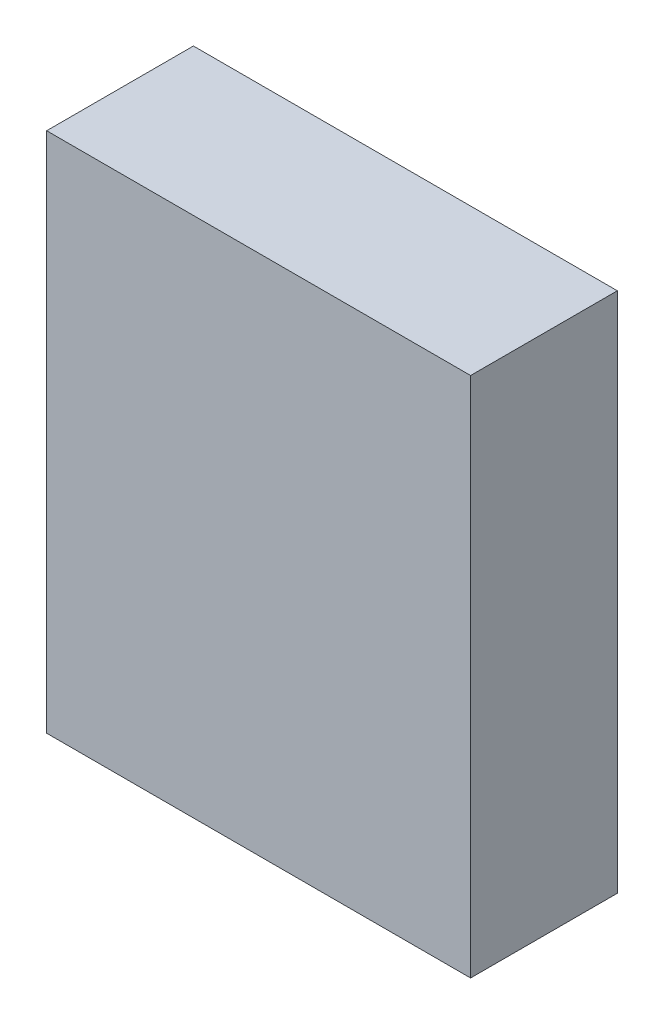
SolidWorks part; units mm, degrees
ref_plane "Front Plane" through (0, 0, 0) normal (0, 0, 1) x (1, 0, 0)
ref_plane "Top Plane" through (0, 0, 0) normal (0, 1, 0) x (1, 0, 0)
ref_plane "Right Plane" through (0, 0, 0) normal (1, 0, 0) x (0, 0, -1)
sketch "Sketch1" plane through (0, 0, 0) normal (0, 0, 1) x (1, 0, 0)
  line L1 (0, 0) -> (26, 0)
  line L2 (0, 0) -> (0, -32)
  line L3 (0, -32) -> (26, -32)
  line L4 (26, 0) -> (26, -32)
  dimension "D1" = 32
  dimension "D2" = 26
extrude "Boss-Extrude1" add sketch "Sketch1" along normal blind 9
